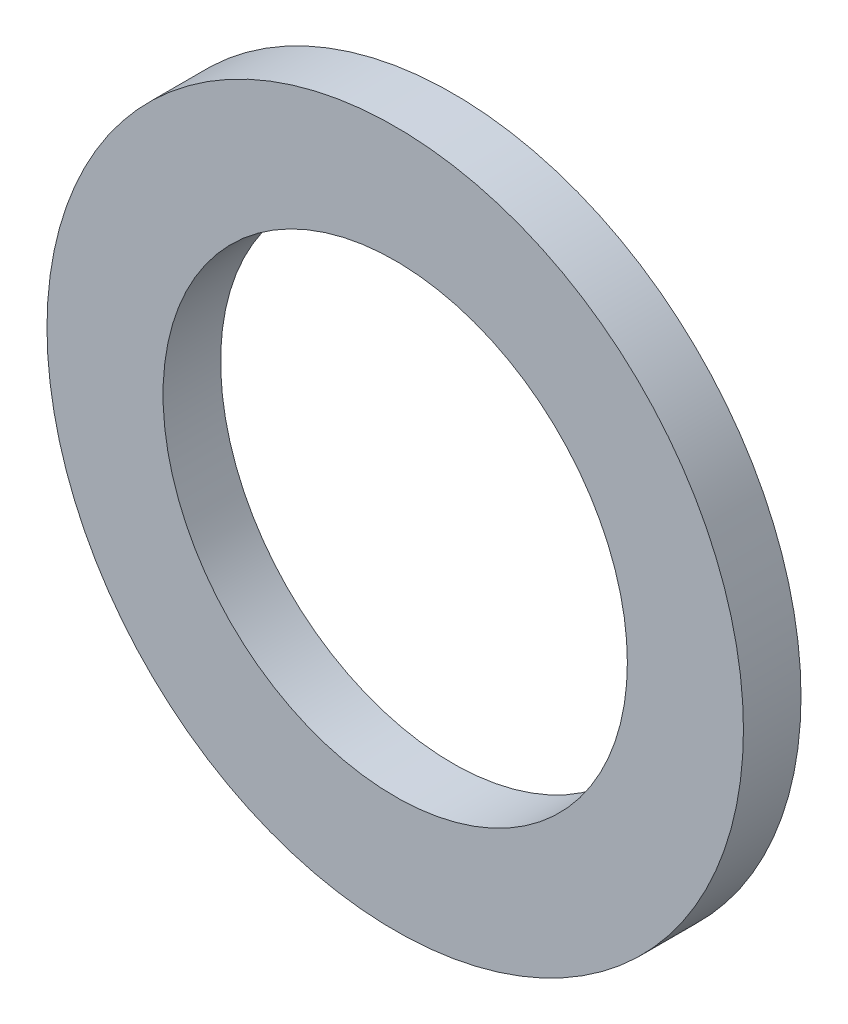
SolidWorks part; units mm, degrees
material "Plain Carbon Steel"
ref_plane "Front Plane" through (0, 0, 0) normal (0, 0, 1) x (1, 0, 0)
ref_plane "Top Plane" through (0, 0, 0) normal (0, 1, 0) x (1, 0, 0)
ref_plane "Right Plane" through (0, 0, 0) normal (1, 0, 0) x (0, 0, -1)
sketch "Sketch1" plane through (0, 0, 0) normal (0, 0, 1) x (1, 0, 0)
  circle A0 centre (0, 0) radius 3.175
  circle A1 centre (0, 0) radius 4.7625
  dimension "D1" = 6.35
  dimension "D2" = 9.525
extrude "Boss-Extrude1" add sketch "Sketch1" along normal blind 0.7874
